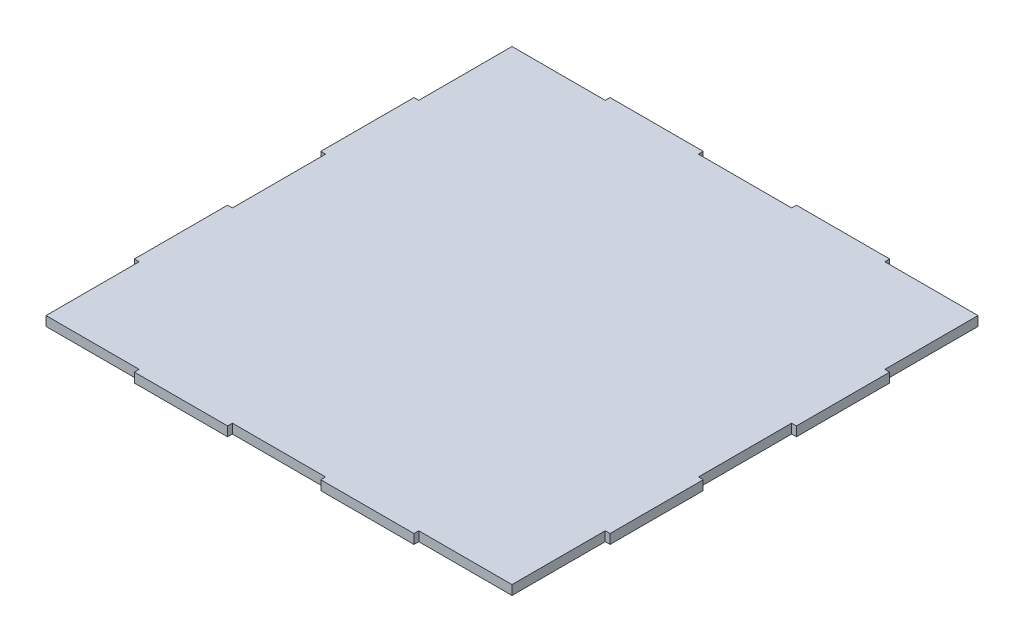
SolidWorks part; units mm, degrees
material "Acrylic (Medium-high impact)"
ref_plane "Front Plane" through (0, 0, 0) normal (0, 0, 1) x (1, 0, 0)
ref_plane "Top Plane" through (0, 0, 0) normal (0, 1, 0) x (1, 0, 0)
ref_plane "Right Plane" through (0, 0, 0) normal (1, 0, 0) x (0, 0, -1)
sketch "Sketch1" plane through (0, 0, 0) normal (0, 1, 0) x (1, 0, 0)
  line L0 (0, 0) -> (59.0804, 0)
  line L1 (59.0804, 0) -> (59.0804, -3.048)
  line L2 (59.0804, -3.048) -> (118.1608, -3.048)
  line L3 (118.1608, -3.048) -> (118.1608, 0)
  line L4 (118.1608, 0) -> (177.2412, 0)
  line L5 (177.2412, 0) -> (177.2412, -3.048)
  line L6 (177.2412, -3.048) -> (236.3216, -3.048)
  line L7 (236.3216, -3.048) -> (236.3216, 0)
  line L8 (236.3216, 0) -> (295.402, 0)
  line L9 (0, 0) -> (59.0804, 59.0804) construction
  line L10 (295.402, 0) -> (236.3216, 59.0804) construction
  line L11 (0, 236.3216) -> (0, 295.402)
  line L12 (-3.048, 236.3216) -> (0, 236.3216)
  line L13 (-3.048, 177.2412) -> (-3.048, 236.3216)
  line L14 (0, 177.2412) -> (-3.048, 177.2412)
  line L15 (0, 118.1608) -> (0, 177.2412)
  line L16 (-3.048, 118.1608) -> (0, 118.1608)
  line L17 (-3.048, 59.0804) -> (-3.048, 118.1608)
  line L18 (0, 59.0804) -> (-3.048, 59.0804)
  line L19 (0, 0) -> (0, 59.0804)
  line L20 (295.402, 59.0804) -> (295.402, 0)
  line L21 (298.45, 59.0804) -> (295.402, 59.0804)
  line L22 (298.45, 118.1608) -> (298.45, 59.0804)
  line L23 (295.402, 118.1608) -> (298.45, 118.1608)
  line L24 (295.402, 177.2412) -> (295.402, 118.1608)
  line L25 (298.45, 177.2412) -> (295.402, 177.2412)
  line L26 (298.45, 236.3216) -> (298.45, 177.2412)
  line L27 (295.402, 236.3216) -> (298.45, 236.3216)
  line L28 (295.402, 295.402) -> (295.402, 236.3216)
  line L29 (295.402, 295.402) -> (236.3216, 295.402)
  line L30 (236.3216, 295.402) -> (236.3216, 298.45)
  line L31 (236.3216, 298.45) -> (177.2412, 298.45)
  line L32 (177.2412, 298.45) -> (177.2412, 295.402)
  line L33 (177.2412, 295.402) -> (118.1608, 295.402)
  line L34 (118.1608, 295.402) -> (118.1608, 298.45)
  line L35 (118.1608, 298.45) -> (59.0804, 298.45)
  line L36 (59.0804, 298.45) -> (59.0804, 295.402)
  line L37 (59.0804, 295.402) -> (0, 295.402)
  dimension "D1" = 45
  dimension "D2" = 59.0804
  dimension "D3" = 3.048
extrude "Boss-Extrude1" add sketch "Sketch1" along normal blind 5.9944 contours L24 L23 L22 L21 L20 L8 L7 L6 L5 L4 L3 L2 L1 L0 L19 L18 L17 L16 L15 L14 L13 L12 L11 L37 L36 L35 L34 L33 L32 L31 L30 L29 L28 L27 L26 L25
